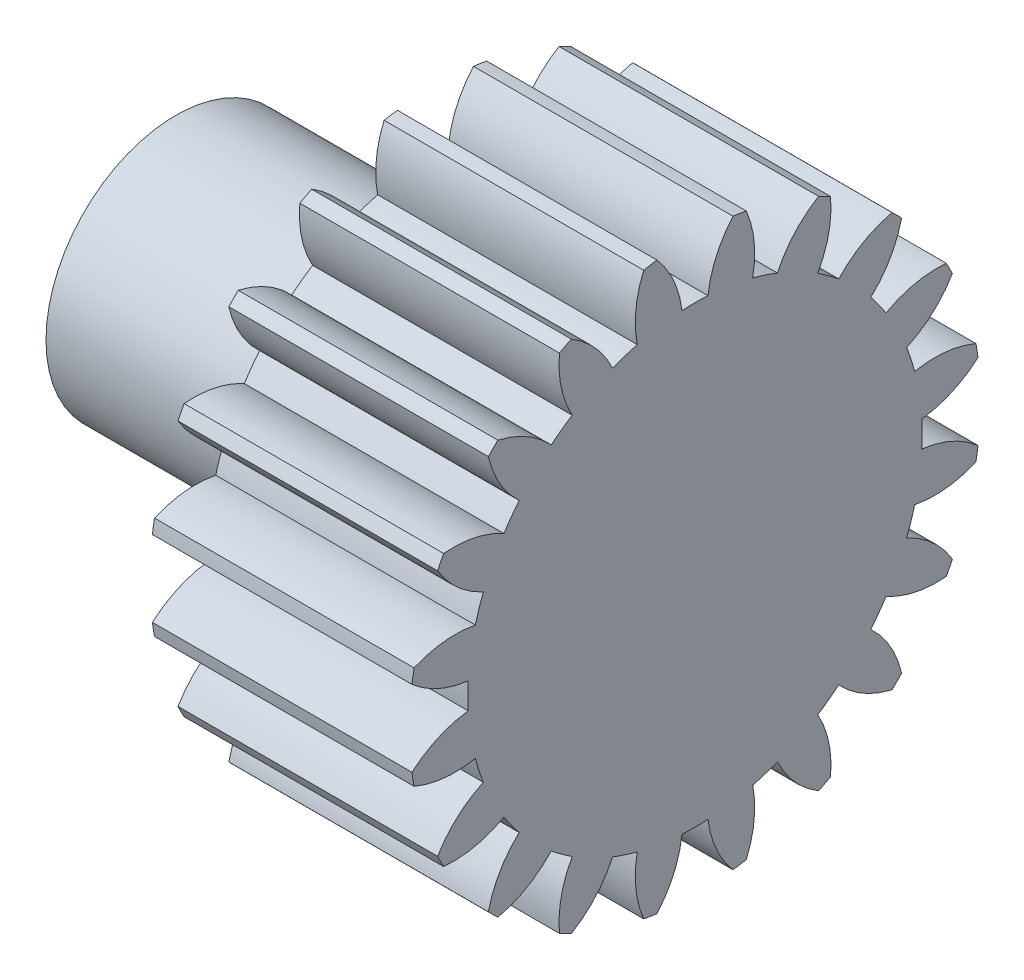
SolidWorks part; units mm, degrees
ref_plane "Plane1" through (0, 0, 0) normal (0, 0, 1) x (1, 0, 0)
ref_plane "Plane2" through (0, 0, 0) normal (0, 1, 0) x (1, 0, 0)
ref_plane "Plane3" through (0, 0, 0) normal (1, 0, 0) x (0, 0, -1)
other "Configuration Table"
sketch "HoldingSke" plane through (0, 0, 0) normal (0, 1, 0) x (1, 0, 0)
  line L0 (0, 0) -> (0.9397, -0.342)
  line L1 (-15, 0) -> (100, 0) construction
  line L2 (0, 0) -> (-2.1039, 2.3779)
  line L3 (0, 0) -> (-11.863, 4.5341)
  line L4 (0, 0) -> (8.1152, 2.9537)
  line L5 (0, 0) -> (-46.8476, -17.4728)
  line L6 (0, 0) -> (-8.2896, -5.593)
  line L7 (-2.1039, 2.3779) -> (8.6586, 51.2059)
  line L8 (-76.2, 54.61) -> (-76.1, 54.61)
  line L9 (-71.009, 38.7566) -> (-53.1078, 45.2721)
  line L10 (-76.2, 71.12) -> (104.1128, 71.12)
  line L11 (0, 0) -> (-10, 0)
  line L12 (-76.2, 101.6) -> (-76.162, 101.6)
  line L13 (24.9733, 27.94) -> (52.9518, 28.4284)
  line L14 (24.9733, 27.94) -> (24.9743, 27.94)
  line L15 (24.9733, 27.94) -> (100.4006, 29.5858)
  line L16 (-63.627, -1) -> (-12.827, -1)
  circle A0 centre (0, 0) radius 0.5
  circle A1 centre (0, 0) radius 8.749
  circle A2 centre (0, 0) radius 37.5
  circle A3 centre (0, 0) radius 0.5
  dimension "MHD" = 17.498
  dimension "Hub_dia" = 75
  dimension "Bore" = 1
  dimension "MBD" = 1
  dimension "Num_teeth" = 20
  dimension "Pitch" = 1
  dimension "Overall_len" = 50
  dimension "Show_teeth" = 20
  dimension "Thickness" = 10
  dimension "OAL" = 50.0001
  dimension "T_dim" = 0.1
  dimension "Ap" = 20
  dimension "H" = 19.05
  dimension "Pitch_radius" = 180.3128
  dimension "Width" = 10
  dimension "Backlash" = 0.038
  dimension "Addendum_fac" = 1
  dimension "Dedendum_fac" = 1.25
  dimension "Clearance_fac" = 0.25
  dimension "Dedendum_add" = 0.001
  dimension "Module" = 1
sketch "BasProSke" plane through (0, 0, 0) normal (0, 1, 0) x (1, 0, 0)
  line L0 (-10, 0) -> (60, 0) construction
  line L1 (0, 0) -> (0, 11)
  line L2 (0, 0) -> (10, 0)
  line L3 (10, 0) -> (10, 11)
  line L4 (10, 11) -> (0, 11)
  dimension "Thickness" = 10
  dimension "Diameter" = 22
revolve "Base-Revolve" add sketch "BasProSke" angle 360 about L0
sketch "TooCutSke" plane through (0, 0, 0) normal (1, 0, 0) x (0, 0, -1)
  line L1 (0, 0) -> (0, 107) construction
  line L2 (0, 0) -> (-0.8511, 9.9637) construction
  line L3 (0, 0) -> (-3.1206, 19.7028) construction
  line L4 (-0.8511, 9.9637) -> (-1.5603, 9.8514) construction
  arc A0 (0.4999, 8.7347) -> (-0.4999, 8.7347) centre (0, 0) ccw
  arc A1 (1.4852, 10.9249) -> (-1.4852, 10.9249) centre (0, 0) ccw
  circle A2 centre (0, 0) radius 10 construction
  circle A3 centre (0, 0) radius 9.3969 construction
  arc A4 (-0.4999, 8.7347) -> (-1.4852, 10.9249) centre (-4.4722, 8.2645) ccw
  arc A5 (1.4852, 10.9249) -> (0.4999, 8.7347) centre (4.4722, 8.2645) ccw
  dimension "Root_dia" = 17.498
  dimension "Overcut_dia" = 22.0508
  dimension "Pitch_dia" = 20
  dimension "Base_dia" = 18.7939
  dimension "Flank_rad" = 4
  dimension "Half_ang" = 9
  dimension "Half_CT" = 0.7181
extrude "ToothCut" cut sketch "TooCutSke" along normal through all
fillet "Breaks" [suppressed] radius 0.02
fillet "RootFillets" [suppressed] radius 0.251
pattern_circular "TeethCuts" count 20 every 18 about axis through (-10, 0, 0) along (1, 0, 0) of "ToothCut", "RootFillets", "Breaks"
sketch "HubNeaOneSke" plane through (0, 0, 0) normal (-1, 0, 0) x (0, 0, 1)
  circle A0 centre (0, 0) radius 8.749
  dimension "Diameter" = 17.498
extrude "HubNearOne" [suppressed] add sketch "HubNeaOneSke" along normal blind 40.0001
sketch "HubNeaBotSke" plane through (0, 0, 0) normal (-1, 0, 0) x (0, 0, 1)
  circle A0 centre (0, 0) radius 8.749
  dimension "Diameter" = 17.498
extrude "HubNearBoth" [suppressed] add sketch "HubNeaBotSke" along normal blind 20
ref_plane "FarPln" through (10, 0, 0) normal (1, 0, 0) x (0, 0, -1)
sketch "HubFarSke" plane through (10, 0, 0) normal (1, 0, 0) x (0, 0, -1)
  circle A0 centre (0, 0) radius 8.749
  dimension "Diameter" = 17.498
extrude "HubFar" [suppressed] add sketch "HubFarSke" along normal blind 20
sketch "BorSke" plane through (0, 0, 0) normal (1, 0, 0) x (0, 0, -1)
  circle A0 centre (0, 0) radius 0.5
  dimension "Diameter" = 1
extrude "Bore" cut sketch "BorSke" along normal mid plane 100.0001
sketch "KeySke" plane through (0, 0, 0) normal (1, 0, 0) x (0, 0, -1)
  line L0 (-0.05, 0) -> (-0.05, 0.6)
  line L1 (-0.05, 0.6) -> (0.05, 0.6)
  line L2 (0.05, 0.6) -> (0.05, 0)
  line L3 (0, 0) -> (0, 34) construction
  line L4 (-0.05, 0) -> (0.05, 0)
  dimension "Offset" = 0.6
  dimension "Width" = 0.1
extrude "Keyway" [suppressed] cut sketch "KeySke" along normal mid plane 100.0001
pattern_circular "Keyway2" [suppressed] count 2 every 90 about axis through (-10, 0, 0) along (1, 0, 0)
sketch "草图1" plane through (10, 0, 0) normal (1, 0, 0) x (0, 0, -1)
  circle A0 centre (0, 0) radius 5
  dimension "D1" = 10
extrude "凸台-拉伸1" add sketch "草图1" against normal blind 20
equation "' \"Module@HoldingSke\" = 6.35"
equation "' \"Num_teeth@HoldingSke\" = 12"
equation "' \"Ap@HoldingSke\" =  20"
equation "' \"Ap@HoldingSke\" = 20"
equation "' \"Width@HoldingSke\" = 0.5 * 25.4"
equation "' \"Hub_dia@HoldingSke\"= 1 * 25.4"
equation "' \"Hub_dia@HoldingSke\" = 1 * 25.4"
equation "' \"Overall_len@HoldingSke\" = 1.0 * 25.4"
equation "' \"Bore@HoldingSke\" = 0.75 * 25.4"
equation "' \"T_dim@HoldingSke\" = 0.1 * 25.4"
equation "' \"Width@KeySke\" = 0.25 * 25.4"
equation "' \"Show_teeth@HoldingSke\" = 13"
equation "' \"Backlash@HoldingSke\" = 0.009 * 25.4"
equation "' \"Addendum_fac@HoldingSke\" = 1.0"
equation "' \"Dedendum_fac@HoldingSke\" = 1.25"
equation "' \"Dedendum_add@HoldingSke\" = 0.00005 * 25.4"
equation "' \"Clearance_fac@HoldingSke\" = 0.25"
equation "\"Pitch@HoldingSke\" = 1 / \"Module@HoldingSke\""
equation "\"Overcut_dia@TooCutSke\" = (\"Num_teeth@HoldingSke\" + 2 * \"Addendum_fac@HoldingSke\") / \"Pitch@HoldingSke\" + 0.002 * 25.4"
equation "\"Pitch_dia@TooCutSke\" = \"Num_teeth@HoldingSke\" / \"Pitch@HoldingSke\""
equation "\"Base_dia@TooCutSke\" = \"Num_teeth@HoldingSke\" / \"Pitch@HoldingSke\" * cos((\"Ap@HoldingSke\"  * 3.14159265 / 180))"
equation "\"Root_dia@TooCutSke\" = (\"Num_teeth@HoldingSke\" + 2) / \"Pitch@HoldingSke\" - 2 * (\"Addendum_fac@HoldingSke\" + \"Dedendum_fac@HoldingSke\") / \"Pitch@HoldingSke\" - \"Dedendum_add@HoldingSke\" * 2"
equation "\"Half_ang@TooCutSke\" = 180 / \"Num_teeth@HoldingSke\""
equation "\"Half_CT@TooCutSke\" = \"Num_teeth@HoldingSke\" / \"Pitch@HoldingSke\" * sin((3.14159265 / 2 / \"Num_teeth@HoldingSke\")) / 2 - 7 * \"Backlash@HoldingSke\" / 4"
equation "\"Flank_rad@TooCutSke\" = \"Num_teeth@HoldingSke\" / \"Pitch@HoldingSke\" / 5"
equation "\"Radius@RootFillets\" = \"Clearance_fac@HoldingSke\" / \"Pitch@HoldingSke\" + \"Dedendum_add@HoldingSke\""
equation "\"Break_rad@Breaks\" = 0.02 / \"Pitch@HoldingSke\""
equation "\"Thickness@HoldingSke\" = \"Width@HoldingSke\""
equation "\"OAL@HoldingSke\" = \"Thickness@HoldingSke\""
equation "\"MHD@HoldingSke\" = (\"Num_teeth@HoldingSke\" + 2) / \"Pitch@HoldingSke\" - 2 * (\"Addendum_fac@HoldingSke\" + \"Dedendum_fac@HoldingSke\")  / \"Pitch@HoldingSke\" - \"Dedendum_add@HoldingSke\" * 2"
equation "\"MBD@HoldingSke\" = (\"Num_teeth@HoldingSke\" + 2) / \"Pitch@HoldingSke\" - 2 * (\"Addendum_fac@HoldingSke\" + \"Dedendum_fac@HoldingSke\")  / \"Pitch@HoldingSke\" - \"Dedendum_add@HoldingSke\" * 2 - 0.002 * 25.4"
equation "\"MHD@HoldingSke\" = ((sgn( \"MHD@HoldingSke\" - \"Hub_dia@HoldingSke\" )-1)*( \"MHD@HoldingSke\" - \"Hub_dia@HoldingSke\" ))/-2+ \"Hub_dia@HoldingSke\""
equation "\"MBD@HoldingSke\" = ((sgn( \"MBD@HoldingSke\" - \"Bore@HoldingSke\" )-1)*( \"MBD@HoldingSke\" - \"Bore@HoldingSke\" ))/-2+ \"Bore@HoldingSke\""
equation "\"OAL@HoldingSke\" = ((sgn( \"OAL@HoldingSke\" - \"Overall_len@HoldingSke\" )+1)*( \"OAL@HoldingSke\" - \"Overall_len@HoldingSke\" ))/2 + \"Overall_len@HoldingSke\" + 0.000002 * 25.4"
equation "\"Num_teeth@TeethCuts\" = int( \"Show_teeth@HoldingSke\" ) + 1"
equation "\"Num_teeth@TeethCuts\" = ((sgn( \"Num_teeth@TeethCuts\" - \"Num_teeth@HoldingSke\" )-1)*( \"Num_teeth@TeethCuts\" - \"Num_teeth@HoldingSke\" ))/-2+ \"Num_teeth@HoldingSke\""
equation "\"Num_teeth@TeethCuts\" = ((sgn( \"Num_teeth@TeethCuts\" - 2.0)+1)*( \"Num_teeth@TeethCuts\" - 2.0))/2 +2.0"
equation "\"Angle@TeethCuts\" = 360.0 / \"Num_teeth@HoldingSke\""
equation "\"Diameter@BasProSke\" = (\"Num_teeth@HoldingSke\" + 2 * \"Addendum_fac@HoldingSke\") / \"Pitch@HoldingSke\""
equation "\"Thickness@BasProSke\"  = \"Thickness@HoldingSke\""
equation "' \"Fillet_rad@BasProSke\" =  \"Thickness@HoldingSke\" * 0.05"
equation "' \"Fillet_rad@BasProSke\" = \"Thickness@HoldingSke\" * 0.05"
equation "\"MHD@HoldingSke\" = ((sgn( \"MHD@HoldingSke\" - \"Root_dia@TooCutSke\" )-1)*( \"MHD@HoldingSke\" - \"Root_dia@TooCutSke\" ))/-2+ \"Root_dia@TooCutSke\""
equation "\"Diameter@HubNeaOneSke\" = \"MHD@HoldingSke\""
equation "\"Length@HubNearOne\" = \"OAL@HoldingSke\" - \"Thickness@BasProSke\""
equation "\"Diameter@HubNeaBotSke\" = \"MHD@HoldingSke\""
equation "\"Length@HubNearBoth\" = ( \"OAL@HoldingSke\" - \"Thickness@BasProSke\" ) / 2.0"
equation "\"Thickness@FarPln\" = \"Thickness@BasProSke\""
equation "\"Diameter@HubFarSke\" = \"MHD@HoldingSke\""
equation "\"Length@HubFar\" = ( \"OAL@HoldingSke\" - \"Thickness@BasProSke\" ) / 2.0"
equation "\"Diameter@BorSke\" = \"MBD@HoldingSke\""
equation "\"D1@Bore\" = \"OAL@HoldingSke\" * 2.0"
equation "\"D1@Keyway\" = \"OAL@HoldingSke\" * 2.0"
equation "\"Offset@KeySke\" = \"T_dim@HoldingSke\" + \"MBD@HoldingSke\" / 2.0"
